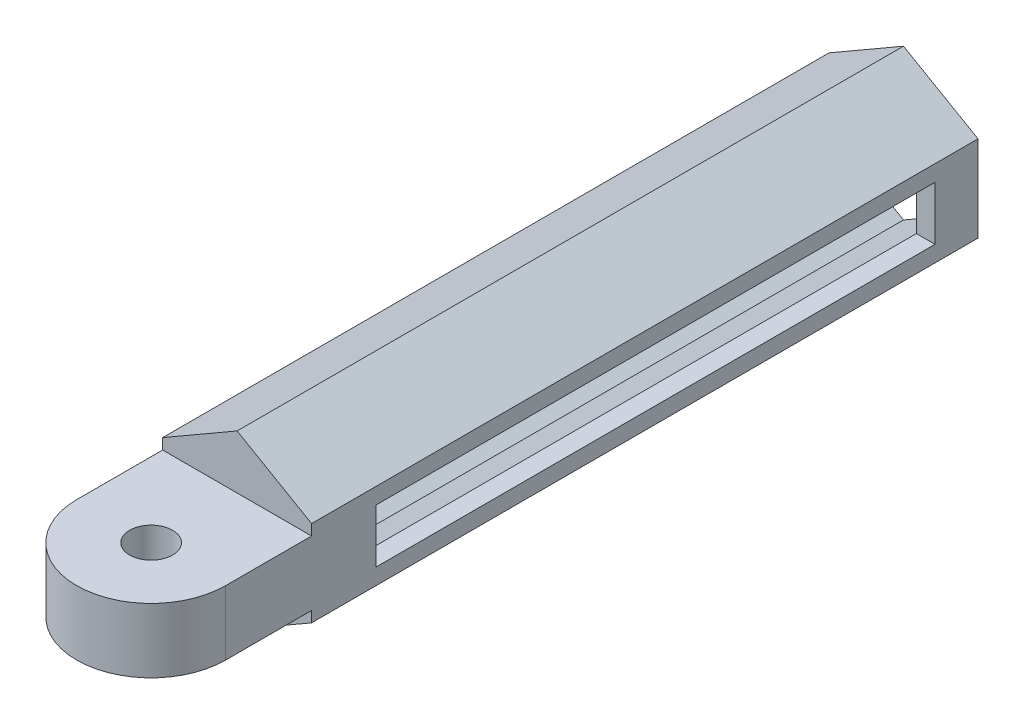
SolidWorks part; units mm, degrees
ref_plane "정면" through (0, 0, 0) normal (0, 0, 1) x (1, 0, 0)
ref_plane "윗면" through (0, 0, 0) normal (0, 1, 0) x (1, 0, 0)
ref_plane "우측면" through (0, 0, 0) normal (1, 0, 0) x (0, 0, -1)
sketch "스케치1" plane through (0, 0, 0) normal (0, 0, 1) x (1, 0, 0)
  line L1 (0, 4) -> (-3.4641, 2)
  line L2 (-3.4641, 2) -> (-3.4641, -2)
  line L3 (-3.4641, -2) -> (0, -4)
  line L4 (0, -4) -> (3.4641, -2)
  line L5 (3.4641, -2) -> (3.4641, 2)
  line L6 (3.4641, 2) -> (0, 4)
  line L7 (0, 3) -> (-2.5981, 1.5)
  line L8 (-2.5981, 1.5) -> (-2.5981, -1.5)
  line L9 (-2.5981, -1.5) -> (0, -3)
  line L10 (0, -3) -> (2.5981, -1.5)
  line L11 (2.5981, -1.5) -> (2.5981, 1.5)
  line L12 (2.5981, 1.5) -> (0, 3)
  circle A0 centre (0, 0) radius 3.4641 construction
  circle A1 centre (0, 0) radius 2.5981 construction
  point P1 (0, 0)
  point P17 (0, 0)
  dimension "D1" = 8
  dimension "D2" = 1
extrude "보스-돌출1" add sketch "스케치1" along normal blind 30
sketch "스케치3" plane through (3.4641, 0, 0) normal (1, 0, 0) x (0, 0, -1)
  line L1 (-28, 1.25) -> (-2, 1.25)
  line L2 (-28, 1.25) -> (-28, -1.25)
  line L3 (-28, -1.25) -> (-2, -1.25)
  line L4 (-2, 1.25) -> (-2, -1.25)
  line L7 (-30, -2) -> (-30, 2) construction
  line L8 (0, -2) -> (0, 2) construction
  point P4 (0, 0)
  point P5 (0, 0)
  point P6 (-29.6203, 1.2509)
  point P7 (-1.7752, -1.25)
  point P9 (-28, 0)
  point P12 (-30, 0)
  dimension "D1" = 2.5
  dimension "D2" = 2
  dimension "D3" = 2
sketch "스케치4" plane through (0, 0, 30) normal (0, 0, 1) x (1, 0, 0)
  line L1 (0, 4) -> (-3.4641, 2)
  line L2 (-3.4641, 2) -> (-3.4641, -2)
  line L3 (-3.4641, -2) -> (0, -4)
  line L4 (0, -4) -> (3.4641, -2)
  line L5 (3.4641, -2) -> (3.4641, 2)
  line L6 (3.4641, 2) -> (0, 4)
  circle A0 centre (0, 0) radius 3.4641 construction
  point P1 (7.2588, 1.2576)
  point P10 (0, 0)
extrude "보스-돌출2" add sketch "스케치4" along normal blind 1
extrude "컷-돌출1" cut sketch "스케치3" against normal up to surface (6.9282 mm away) up to face at (-3.4641, 0, 15.5)
sketch "스케치7" plane through (0, 0, 0) normal (0, 1, 0) x (1, 0, 0)
  line L0 (-3.4641, -31) -> (-3.4641, 0) construction
  line L1 (3.4641, -31) -> (-3.4641, -31)
  line L2 (3.4641, -31) -> (3.4641, -35)
  line L4 (-3.4641, -31) -> (-3.4641, -35)
  arc A0 (-3.4641, -35) -> (3.4641, -35) centre (0, -35) ccw
  circle A1 centre (0, -35) radius 1
  dimension "D1" = 4
  dimension "D2" = 2
extrude "보스-돌출3" add sketch "스케치7" along normal blind 1.5 and the other way blind 1.5
